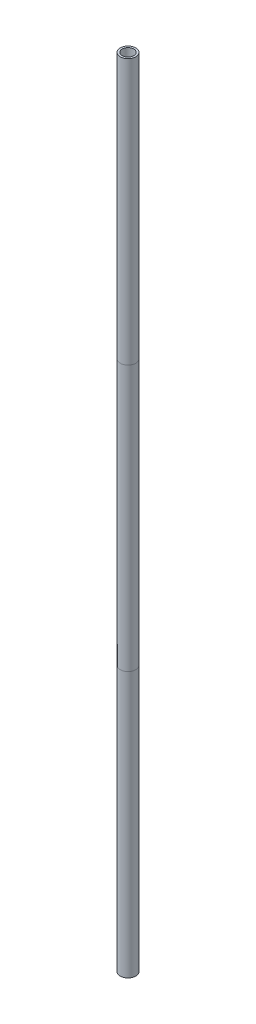
SolidWorks part; units mm, degrees
material "AISI Type 316L stainless steel"
ref_plane "Front Plane" through (0, 0, 0) normal (0, 0, 1) x (1, 0, 0)
ref_plane "Top Plane" through (0, 0, 0) normal (0, 1, 0) x (1, 0, 0)
ref_plane "Right Plane" through (0, 0, 0) normal (1, 0, 0) x (0, 0, -1)
sketch "Sketch1" plane through (0, 0, 0) normal (0, 1, 0) x (1, 0, 0)
  circle A0 centre (0, 0) radius 19.5
  circle A1 centre (0, 0) radius 14.5
  dimension "D1" = 39
  dimension "D2" = 5
extrude "Boss-Extrude1" add sketch "Sketch1" along normal blind 2000
sketch "Sketch2" plane through (0, 0, 0) normal (0, 0, 1) x (1, 0, 0)
  line L0 (-19.5, 1333.3333) -> (19.5, 1333.3333)
  line L1 (-19.5, 2000) -> (-19.5, 0) construction
  line L2 (19.5, 0) -> (19.5, 2000) construction
  line L3 (-19.5, 666.6667) -> (19.5, 666.6667)
  line L4 (0, 2000) -> (0, 1333.3333) construction
  line L5 (19.5, 2000) -> (-19.5, 2000) construction
  line L6 (0, 1333.3333) -> (0, 666.6667) construction
  line L7 (0, 666.6667) -> (0, 0) construction
split "Split1" trim tools "Sketch2" bodies to split 101 resulting bodies 102 103 104
